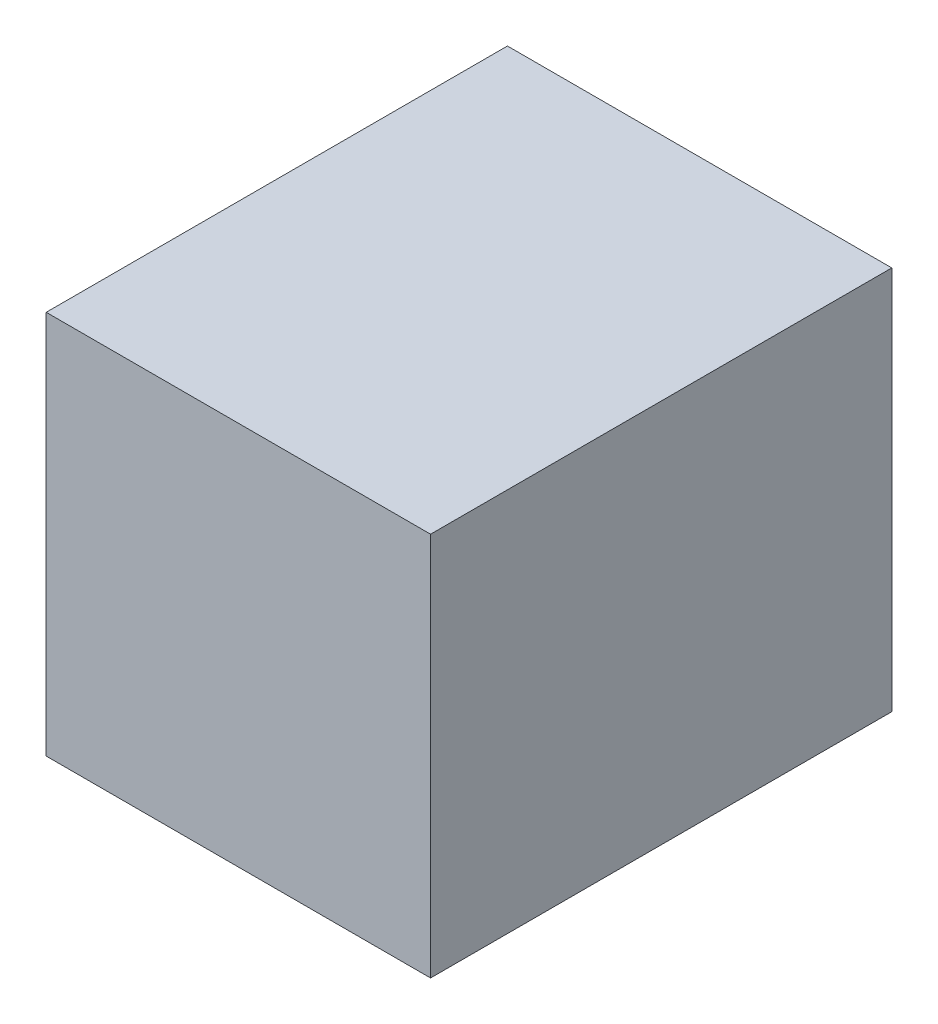
SolidWorks part; units mm, degrees
ref_plane "Front Plane" through (0, 0, 0) normal (0, 0, 1) x (1, 0, 0)
ref_plane "Top Plane" through (0, 0, 0) normal (0, 1, 0) x (1, 0, 0)
ref_plane "Right Plane" through (0, 0, 0) normal (1, 0, 0) x (0, 0, -1)
sketch "Sketch1" plane through (0, 0, 0) normal (0, 0, 1) x (1, 0, 0)
  line L1 (-2.5, -2.5) -> (2.5, -2.5)
  line L2 (-2.5, -2.5) -> (-2.5, 2.5)
  line L3 (-2.5, 2.5) -> (2.5, 2.5)
  line L4 (2.5, -2.5) -> (2.5, 2.5)
  line L5 (-2.5, -2.5) -> (2.5, 2.5) construction
  line L6 (-2.5, 2.5) -> (2.5, -2.5) construction
  point P0 (0, 0)
  dimension "D1" = 5
  dimension "D2" = 5
extrude "Boss-Extrude1" add sketch "Sketch1" along normal blind 6
